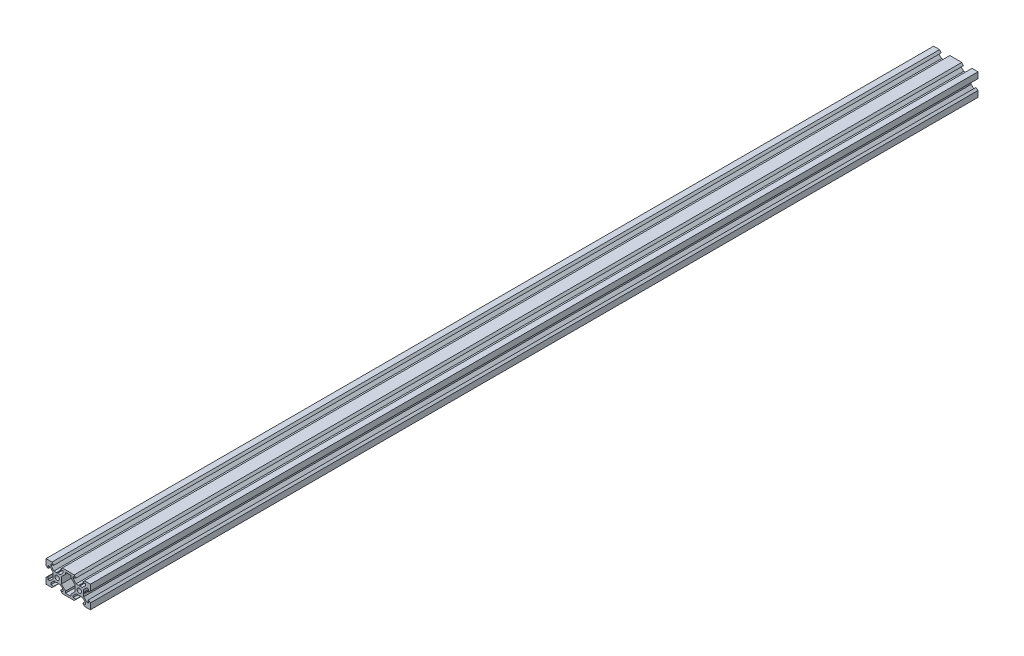
SolidWorks part; units mm, degrees
ref_plane "Front Plane" through (0, 0, 0) normal (0, 0, 1) x (1, 0, 0)
ref_plane "Top Plane" through (0, 0, 0) normal (0, 1, 0) x (1, 0, 0)
ref_plane "Right Plane" through (0, 0, 0) normal (1, 0, 0) x (0, 0, -1)
sketch "Sketch1" plane through (0, 0, 0) normal (0, 0, 1) x (1, 0, 0)
  line L0 (-5.3896, 10) -> (5.3896, 10)
  line L1 (0, 10) -> (0, 4.6104) construction
  line L2 (-6.1, -2.8393) -> (-2.3769, -6.5562)
  line L3 (5.3896, -10) -> (-5.3896, -10) construction
  line L5 (-6.1, 2.8393) -> (-6.1, -2.8393)
  line L6 (-4.5, 8.2) -> (-4.5, 6.5562)
  line L7 (2.3832, 6.5562) -> (2.3832, 8.2)
  line L9 (-6.1, 2.8393) -> (-2.3832, 6.5562)
  line L10 (-4.5, 6.5562) -> (-7.1607, 3.9)
  line L11 (-2.3832, 6.5562) -> (-2.3832, 8.2)
  line L12 (-5.3896, 10) -> (-6.9, 8.2)
  line L13 (6.1, 2.8393) -> (2.3832, 6.5562)
  line L14 (-6.9, 8.2) -> (-4.5, 8.2)
  line L15 (-16.5562, 5.5) -> (-18.2, 5.5)
  line L16 (0, 0) -> (6.1, 0) construction
  line L17 (-6.9, -8.2) -> (-4.5, -8.2)
  line L18 (-2.3769, -6.5562) -> (-2.3769, -8.2)
  line L19 (-5.3896, -10) -> (-6.9, -8.2)
  line L20 (2.3769, -6.5562) -> (2.3769, -8.2)
  line L21 (-9.4804, -3.9002) -> (-10, -3.6002)
  line L22 (-9.4804, 3.8998) -> (-10, 3.5998)
  line L23 (6.1, -2.8393) -> (2.3769, -6.5562)
  line L24 (-2.3769, -8.2) -> (2.3769, -8.2)
  line L25 (-2.3832, 8.2) -> (2.3832, 8.2)
  line L26 (-9.4804, 3.8998) -> (-7.1607, 3.9)
  line L27 (-5.3896, -10) -> (5.3896, -10)
  line L28 (-9.4804, -3.9002) -> (-7.1604, -3.9002)
  line L29 (-4.5, -6.5562) -> (-7.1607, -3.9)
  line L30 (-20, 10) -> (20, 10) construction
  line L32 (6.1, 2.8393) -> (6.1, -2.8393)
  line L33 (-4.5, -8.2) -> (-4.5, -6.5562)
  line L34 (-16.5562, -5.5) -> (-18.2, -5.5)
  line L36 (-10, 0) -> (-10, 8.2) construction
  line L37 (-20, -10) -> (-14.6104, -10) construction
  line L38 (-20, -10) -> (-20, -4.6104) construction
  line L39 (-20, 10) -> (-20, 4.6104) construction
  line L40 (-20, 10) -> (-14.6104, 10) construction
  line L41 (-20, -10) -> (-20, -4.6104)
  line L42 (-15.5, -8.2) -> (-15.5, -6.5562)
  line L43 (-20, -10) -> (-14.6104, -10)
  line L44 (7.1519, 3.8998) -> (9.4804, 3.8998)
  line L45 (-16.5562, -5.5) -> (-13.9, -2.8393)
  line L46 (-15.5, -6.5562) -> (-12.8393, -3.9)
  line L47 (-12.8393, -3.9) -> (-10.5196, -3.9002)
  line L48 (-13.9, -2.8393) -> (-13.9, -0.5196)
  line L49 (-12.8393, 3.9) -> (-10.5196, 3.8998)
  line L50 (-13.9, 0.5196) -> (-13.9, 2.8393)
  line L51 (-13.9, 0.5196) -> (-13.6, 0)
  line L52 (-13.6, 0) -> (-13.9, -0.5196)
  line L53 (-10.5196, 3.8998) -> (-10, 3.5998)
  line L54 (-10.5196, -3.9002) -> (-10, -3.6002)
  line L55 (-20, -4.6104) -> (-18.2, -3.1)
  line L56 (-14.6104, -10) -> (-13.1, -8.2)
  line L57 (-18.2, -3.1) -> (-18.2, -5.5)
  line L58 (-13.1, -8.2) -> (-15.5, -8.2)
  line L59 (-20, -10) -> (20, -10) construction
  line L60 (-20, -10) -> (-20, 10) construction
  line L61 (-13.1, 8.2) -> (-15.5, 8.2)
  line L62 (-18.2, 3.1) -> (-18.2, 5.5)
  line L63 (-14.6104, 10) -> (-13.1, 8.2)
  line L64 (-20, 4.6104) -> (-18.2, 3.1)
  line L65 (-15.5, 6.5562) -> (-12.8393, 3.9)
  line L66 (-16.5562, 5.5) -> (-13.9, 2.8393)
  line L67 (-20, 10) -> (-20, 4.6104)
  line L68 (-20, 10) -> (-14.6104, 10)
  line L69 (-15.5, 8.2) -> (-15.5, 6.5562)
  line L70 (4.5, 6.5562) -> (7.1519, 3.8998)
  line L71 (15.5, 6.5562) -> (12.8481, 3.8998)
  line L72 (0, -10) -> (0, 10) construction
  line L73 (-20, -10) -> (0, 10) construction
  line L74 (10.5196, 3.8998) -> (12.8481, 3.8998)
  line L75 (12.8393, -3.9) -> (10.5192, -3.9)
  line L76 (20, -10) -> (0, 10) construction
  line L77 (20, -10) -> (20, 10) construction
  line L78 (20, 10) -> (14.6104, 10) construction
  line L79 (20, 10) -> (20, 4.6104) construction
  line L80 (20, -10) -> (20, -4.6104) construction
  line L81 (20, -10) -> (14.6104, -10) construction
  line L82 (10, 0) -> (10, 8.2) construction
  line L83 (20, 10) -> (20, 4.6104)
  line L84 (15.5, 8.2) -> (15.5, 6.5562)
  line L85 (20, 10) -> (14.6104, 10)
  line L87 (16.5562, 5.5) -> (13.9, 2.8393)
  line L89 (20, 4.6104) -> (18.2, 3.1)
  line L90 (14.6104, 10) -> (13.1, 8.2)
  line L91 (18.2, 3.1) -> (18.2, 5.5)
  line L92 (13.1, 8.2) -> (15.5, 8.2)
  line L93 (13.1, -8.2) -> (15.5, -8.2)
  line L94 (18.2, -3.1) -> (18.2, -5.5)
  line L95 (14.6104, -10) -> (13.1, -8.2)
  line L96 (20, -4.6104) -> (18.2, -3.1)
  line L97 (10.5196, -3.9002) -> (10, -3.6002)
  line L98 (10.5196, 3.8998) -> (10, 3.5998)
  line L99 (13.6, 0) -> (13.9, -0.5196)
  line L100 (13.9, 0.5196) -> (13.6, 0)
  line L101 (13.9, 0.5196) -> (13.9, 2.8393)
  line L102 (9.4808, -3.9) -> (7.1607, -3.9)
  line L103 (13.9, -2.8393) -> (13.9, -0.5196)
  line L105 (15.5, -6.5562) -> (12.8393, -3.9)
  line L106 (16.5562, -5.5) -> (13.9, -2.8393)
  line L107 (20, -10) -> (20, -4.6104)
  line L108 (20, -10) -> (14.6104, -10)
  line L109 (15.5, -8.2) -> (15.5, -6.5562)
  line L111 (16.5562, -5.5) -> (18.2, -5.5)
  line L112 (4.5, -8.2) -> (4.5, -6.5562)
  line L114 (4.5, -6.5562) -> (7.1607, -3.9)
  line L121 (9.4804, 3.8998) -> (10, 3.5998)
  line L122 (9.4804, -3.9002) -> (10, -3.6002)
  line L124 (5.3896, -10) -> (6.9, -8.2)
  line L126 (6.9, -8.2) -> (4.5, -8.2)
  line L128 (16.5562, 5.5) -> (18.2, 5.5)
  line L129 (6.9, 8.2) -> (4.5, 8.2)
  line L131 (5.3896, 10) -> (6.9, 8.2)
  line L135 (4.5, 8.2) -> (4.5, 6.5562)
  circle A0 centre (-10, 0) radius 2
  circle A1 centre (10, 0) radius 2
  dimension "D14" = 4
  dimension "D1" = 20
  dimension "D2" = 5.3896
  dimension "D3" = 1.8
  dimension "D4" = 1.5104
  dimension "D5" = 4.5
  dimension "D6" = 5.5
  dimension "D7" = 120
  dimension "D8" = 0.3
  dimension "D9" = 2.3197
  dimension "D10" = 7.8
  dimension "D11" = 20
  dimension "D12" = 1.5
  dimension "D13" = 2.6607
  dimension "D15" = 50
  dimension "D16" = 1.5
  dimension "D17" = 1.8
  dimension "D18" = 16.4
  dimension "D19" = 2.3832
  dimension "D20" = 45
extrude "Boss-Extrude1" add sketch "Sketch1" along normal blind 1000
sketch "Sketch2" plane through (0, 0, 1000) normal (0, 0, 1) x (1, 0, 0)
  line L1 (-20, 10) -> (20, 10)
  line L2 (-20, 10) -> (-20, -10)
  line L3 (-20, -10) -> (20, -10)
  line L4 (20, 10) -> (20, -10)
extrude "Cut-Extrude1" cut sketch "Sketch2" against normal offset from surface (200 mm away) 800 up to face at (12, 0, 0)
